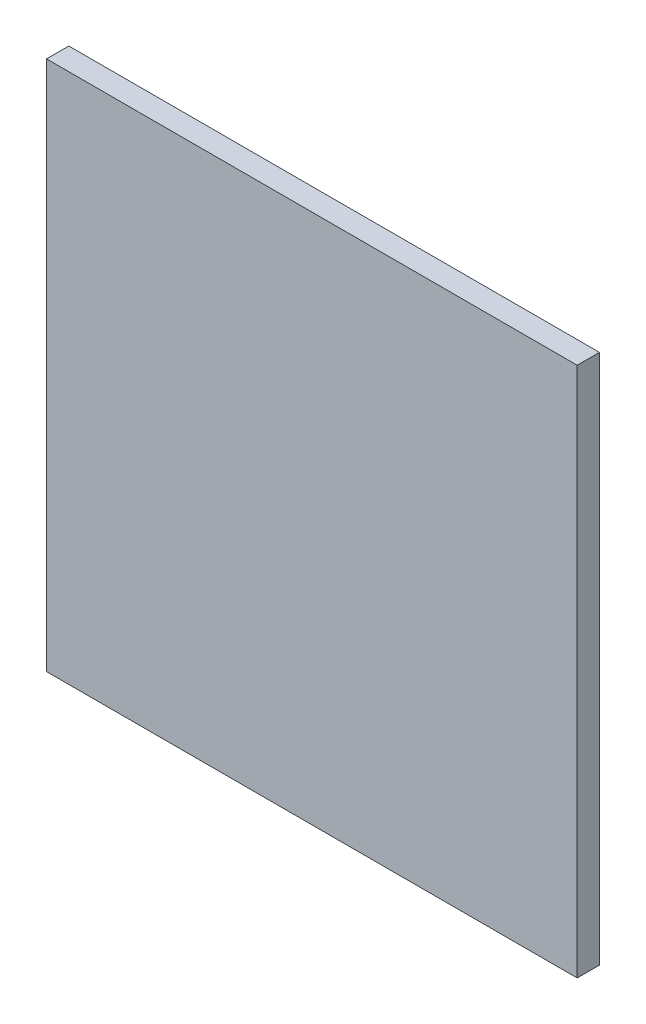
SolidWorks part; units mm, degrees
ref_plane "Front Plane" through (0, 0, 0) normal (0, 0, 1) x (1, 0, 0)
ref_plane "Top Plane" through (0, 0, 0) normal (0, 1, 0) x (1, 0, 0)
ref_plane "Right Plane" through (0, 0, 0) normal (1, 0, 0) x (0, 0, -1)
sketch "Sketch1" plane through (0, 0, 0) normal (0, 0, 1) x (1, 0, 0)
  line L1 (0, 0) -> (71.5, 0)
  line L2 (0, 0) -> (0, 71.5)
  line L3 (0, 71.5) -> (71.5, 71.5)
  line L4 (71.5, 0) -> (71.5, 71.5)
  dimension "D1" = 71.5
  dimension "D2" = 71.5
extrude "Boss-Extrude1" add sketch "Sketch1" along normal blind 3
